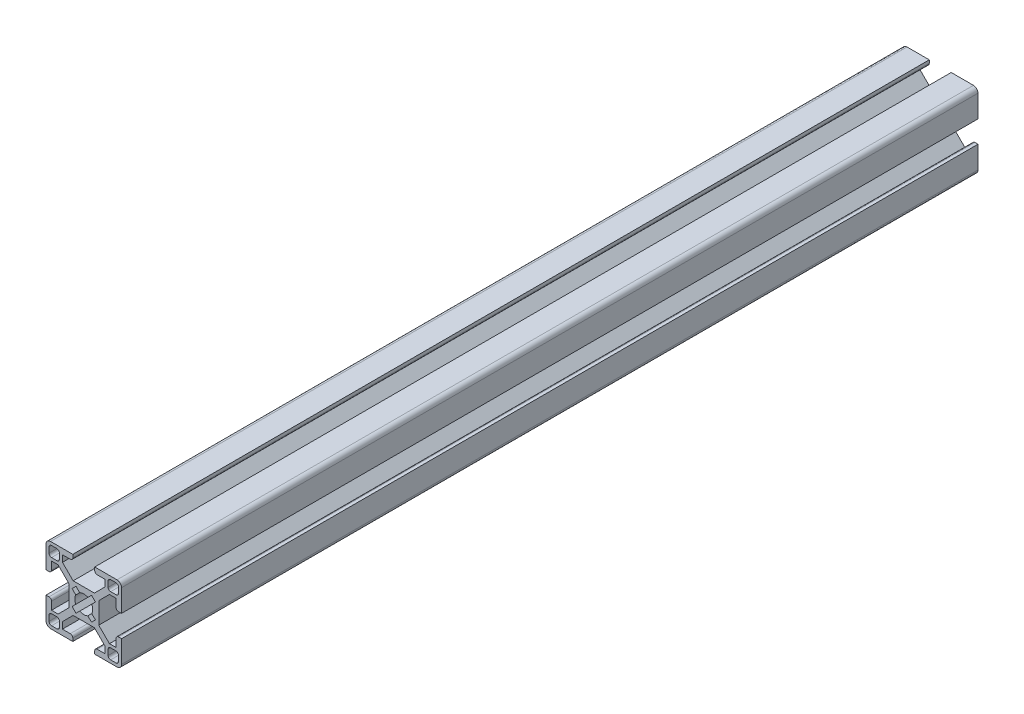
SolidWorks part; units mm, degrees
ref_plane "Front Plane" through (0, 0, 0) normal (0, 0, 1) x (1, 0, 0)
ref_plane "Top Plane" through (0, 0, 0) normal (0, 1, 0) x (1, 0, 0)
ref_plane "Right Plane" through (0, 0, 0) normal (1, 0, 0) x (0, 0, -1)
sketch "Sketch1" plane through (0, 0, 0) normal (0, 0, 1) x (1, 0, 0)
  line L0 (0, 0) -> (5.95, 0) construction
  line L1 (0, 0) -> (0, 5.95) construction
  line L2 (-5.95, 5.95) -> (5.95, 5.95)
  line L3 (5.95, 5.95) -> (5.95, 0)
  line L4 (4.2176, 5.95) -> (8.4602, 10.1926)
  line L5 (5.95, 5.95) -> (8.4425, 8.4425) construction
  line L6 (5.95, 4.2176) -> (10.1926, 8.4602)
  line L7 (8.4602, 12.7926) -> (8.4602, 8.4602)
  line L8 (8.4602, 8.4602) -> (12.7926, 8.4602)
  line L9 (12.7926, 8.4602) -> (12.7926, 5.3502)
  line L10 (13.7926, 4.3502) -> (14.9926, 4.3502)
  line L11 (14.9926, 4.3502) -> (14.9926, 13.1926)
  line L12 (8.4602, 8.4602) -> (14.9926, 14.9926) construction
  line L13 (4.3502, 13.7926) -> (4.3502, 14.9926)
  line L14 (4.3502, 14.9926) -> (13.1926, 14.9926)
  line L15 (5.3502, 12.7926) -> (8.4602, 12.7926)
  line L16 (-9.6602, 9.6602) -> (-13.7926, 13.7926) construction
  line L17 (10.6602, 13.7926) -> (12.7926, 13.7926)
  line L18 (9.6602, 12.7926) -> (9.6602, 10.6602)
  line L19 (10.6602, 9.6602) -> (12.7926, 9.6602)
  line L20 (13.7926, 12.7926) -> (13.7926, 10.6602)
  line L21 (9.6602, 13.7926) -> (13.7926, 9.6602) construction
  line L22 (9.6602, 9.6602) -> (13.7926, 13.7926) construction
  line L23 (-9.6602, 13.7926) -> (-13.7926, 9.6602) construction
  line L24 (-8.4602, 8.4602) -> (-14.9926, 14.9926) construction
  line L25 (-5.95, 5.95) -> (-8.4425, 8.4425) construction
  line L26 (-13.7926, 12.7926) -> (-13.7926, 10.6602)
  line L27 (-10.6602, 9.6602) -> (-12.7926, 9.6602)
  line L28 (-9.6602, 12.7926) -> (-9.6602, 10.6602)
  line L29 (-10.6602, 13.7926) -> (-12.7926, 13.7926)
  line L30 (-5.3502, 12.7926) -> (-8.4602, 12.7926)
  line L31 (-4.3502, 14.9926) -> (-13.1926, 14.9926)
  line L32 (-4.3502, 13.7926) -> (-4.3502, 14.9926)
  line L33 (-14.9926, 4.3502) -> (-14.9926, 13.1926)
  line L34 (-13.7926, 4.3502) -> (-14.9926, 4.3502)
  line L35 (-12.7926, 8.4602) -> (-12.7926, 5.3502)
  line L36 (-8.4602, 8.4602) -> (-12.7926, 8.4602)
  line L37 (-8.4602, 12.7926) -> (-8.4602, 8.4602)
  line L38 (-5.95, 4.2176) -> (-10.1926, 8.4602)
  line L39 (-4.2176, 5.95) -> (-8.4602, 10.1926)
  line L40 (-5.95, 5.95) -> (-5.95, 0)
  line L41 (-5.95, 0) -> (5.95, 0)
  arc A0 (13.1926, 14.9926) -> (14.9926, 13.1926) centre (13.1926, 13.1926) cw
  arc A1 (10.6602, 13.7926) -> (9.6602, 12.7926) centre (10.6602, 12.7926) ccw
  arc A2 (12.7926, 13.7926) -> (13.7926, 12.7926) centre (12.7926, 12.7926) cw
  arc A3 (12.7926, 9.6602) -> (13.7926, 10.6602) centre (12.7926, 10.6602) ccw
  arc A4 (9.6602, 10.6602) -> (10.6602, 9.6602) centre (10.6602, 10.6602) ccw
  arc A5 (4.3502, 13.7926) -> (5.3502, 12.7926) centre (5.3502, 13.7926) ccw
  arc A6 (12.7926, 5.3502) -> (13.7926, 4.3502) centre (13.7926, 5.3502) ccw
  arc A7 (-12.7926, 5.3502) -> (-13.7926, 4.3502) centre (-13.7926, 5.3502) cw
  arc A8 (-4.3502, 13.7926) -> (-5.3502, 12.7926) centre (-5.3502, 13.7926) cw
  arc A9 (-9.6602, 10.6602) -> (-10.6602, 9.6602) centre (-10.6602, 10.6602) cw
  arc A10 (-12.7926, 9.6602) -> (-13.7926, 10.6602) centre (-12.7926, 10.6602) cw
  arc A11 (-12.7926, 13.7926) -> (-13.7926, 12.7926) centre (-12.7926, 12.7926) ccw
  arc A12 (-10.6602, 13.7926) -> (-9.6602, 12.7926) centre (-10.6602, 12.7926) cw
  arc A13 (-13.1926, 14.9926) -> (-14.9926, 13.1926) centre (-13.1926, 13.1926) ccw
  point P12 (11.7264, 11.7264)
  point P40 (4.3502, 12.7926)
  point P43 (12.7926, 4.3502)
  point P82 (-12.7926, 4.3502)
  point P83 (-4.3502, 12.7926)
  point P84 (-11.7264, 11.7264)
  dimension "D9" = 1.8
  dimension "D10" = 1
  dimension "D11" = 1
  dimension "D1" = 5.95
  dimension "D4" = 2.6
  dimension "D2" = 135
  dimension "D3" = 2.45
  dimension "D5" = 6
  dimension "D6" = 4.11
  dimension "D7" = 2.2
  dimension "D8" = 1.2
extrude "Boss-Extrude1" add sketch "Sketch1" against normal blind 340 contours L31 A13 L33 L34 A7 L35 L36 L37 L30 A8 L32 L29 A12 L28 A9 L27 A10 L26 A11 | L40 L2 L39 L37 L36 L38 | L40 L41 L3 L2 | L8 L7 L4 L2 L3 L6 | L9 A6 L10 L11 A0 L14 L13 A5 L15 L7 L8 A4 L18 A1 L17 A2 L20 A3 L19
mirror "Mirror1" about plane through (0, 0, -340) normal (0, -1, 0) of bodies 101
sketch "Sketch2" plane through (0, 0, 0) normal (0, 0, 1) x (1, 0, 0)
  line L0 (-3.0759, -4.6315) -> (4.6315, 3.0759)
  line L1 (-3.0759, -4.6315) -> (-4.6315, -3.0759)
  line L2 (4.6315, 3.0759) -> (3.0759, 4.6315)
  line L3 (-4.6315, -3.0759) -> (3.0759, 4.6315)
  line L4 (-3.0759, -4.6315) -> (3.0759, 4.6315) construction
  line L5 (4.6315, 3.0759) -> (-4.6315, -3.0759) construction
  line L6 (0, 0) -> (0, 2.5254) construction
  line L7 (-4.6315, 3.0759) -> (3.0759, -4.6315)
  line L8 (-4.6315, 3.0759) -> (-3.0759, 4.6315)
  line L9 (-3.0759, 4.6315) -> (4.6315, -3.0759)
  line L10 (3.0759, -4.6315) -> (4.6315, -3.0759)
  line L11 (0, 0) -> (3.0759, 4.6315) construction
  line L12 (0, 0) -> (4.6315, -3.0759) construction
  circle A0 centre (0, 0) radius 3.555
  dimension "D1" = 7.11
  dimension "D2" = 45
  dimension "D3" = 2.2
  dimension "D4" = 10.9
  dimension "D6" = 90
  dimension "D5" = 2
extrude "Cut-Extrude1" cut sketch "Sketch2" against normal through all contours A0 L9 L8 L7 | L9 A0 L7 L3 | L7 A0 L3 | A0 L3 L1 L0 | L3 A0 L0 L7 | L0 A0 L7 | L7 A0 L9 L0 | L9 A0 L0 | L9 L3 L7 L0 | L0 A0 L3 L9 | L3 A0 L9 | A0 L0 L2 L3 | A0 L7 L10 L9
